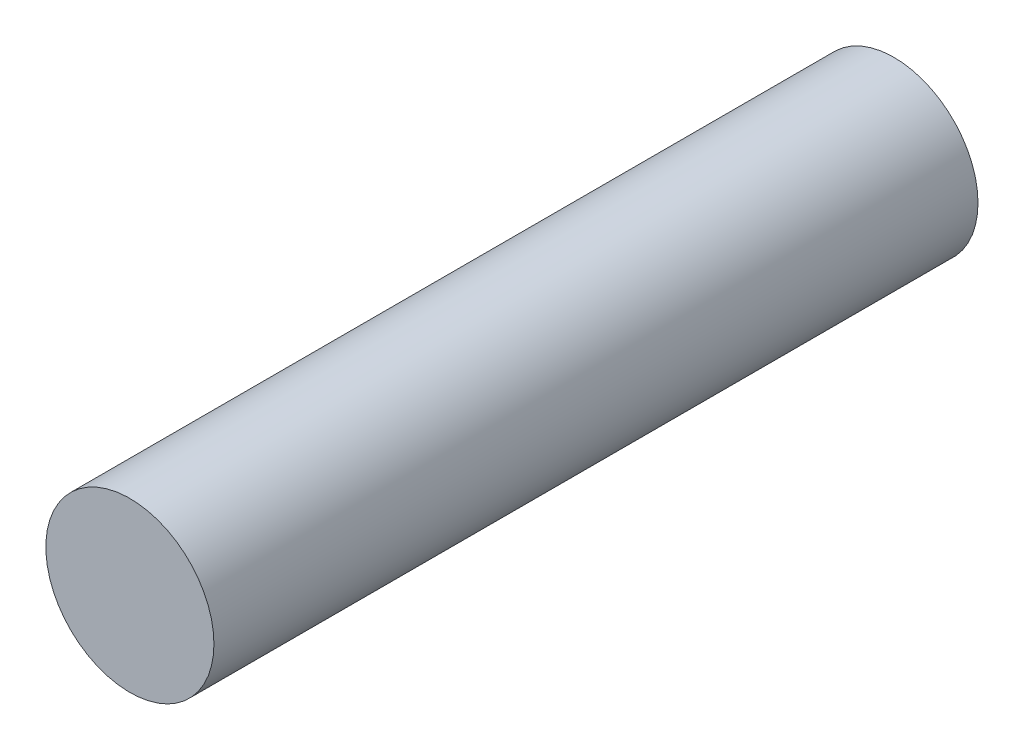
SolidWorks part; units mm, degrees
ref_plane "Płaszczyzna przednia" through (0, 0, 0) normal (0, 0, 1) x (1, 0, 0)
ref_plane "Płaszczyzna górna" through (0, 0, 0) normal (0, 1, 0) x (1, 0, 0)
ref_plane "Płaszczyzna prawa" through (0, 0, 0) normal (1, 0, 0) x (0, 0, -1)
sketch "Szkic1" plane through (0, 0, 0) normal (0, 0, 1) x (1, 0, 0)
  circle A0 centre (0, 0) radius 5.5
extrude "Dodanie-wyciągnięcie1" add sketch "Szkic1" along normal blind 50
